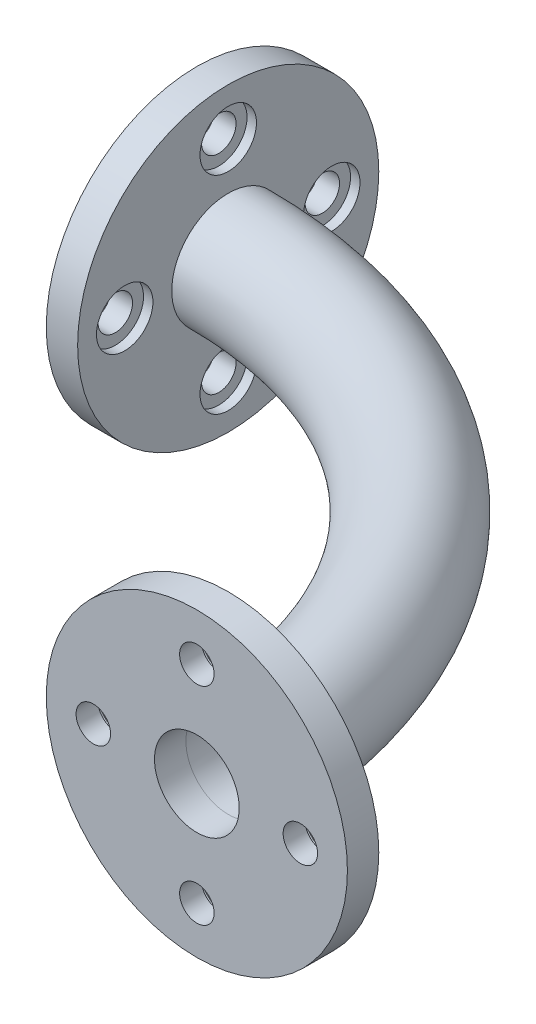
SolidWorks part; units mm, degrees
ref_plane "Alzado" through (0, 0, 0) normal (0, 0, 1) x (1, 0, 0)
ref_plane "Planta" through (0, 0, 0) normal (0, 1, 0) x (1, 0, 0)
ref_plane "Vista lateral" through (0, 0, 0) normal (1, 0, 0) x (0, 0, -1)
sketch "Croquis2" plane through (0, 0, 0) normal (1, 0, 0) x (0, 0, -1)
  circle A0 centre (0, 0) radius 48
  circle A1 centre (0, 0) radius 13.5
  circle A2 centre (0, 33) radius 5.5
  circle A3 centre (33, 0) radius 5.5
  circle A4 centre (0, -33) radius 5.5
  circle A5 centre (-33, 0) radius 5.5
  point P15 (0, 0)
  dimension "D1" = 96
  dimension "D2" = 27
  dimension "D3" = 11
  dimension "D4" = 33
  dimension "D5" = 4
extrude "Saliente-Extruir1" add sketch "Croquis2" along normal blind 10
ref_plane "Plano1" through (0, 0, 150) normal (0, 0, 1) x (1, 0, 0)
sketch "Croquis4" plane through (0, 0, 150) normal (0, 0, 1) x (1, 0, 0)
  circle A0 centre (150, 0) radius 48
  circle A1 centre (150, 0) radius 13.5
  circle A2 centre (150, 33) radius 5.5
  circle A3 centre (183, 0) radius 5.5
  circle A4 centre (150, -33) radius 5.5
  circle A5 centre (117, 0) radius 5.5
  point P5 (0, 0)
  point P6 (171.2712, -22.8328)
  point P7 (0, 0)
  point P11 (150, 0)
  point P16 (150, 0)
  dimension "D1" = 96
  dimension "D2" = 27
  dimension "D3" = 11
  dimension "D4" = 33
  dimension "D5" = 150
  dimension "D6" = 4
extrude "Saliente-Extruir2" add sketch "Croquis4" against normal blind 10 separate body
sketch "Croquis5" plane through (0, 0, 0) normal (0, 1, 0) x (1, 0, 0)
  line L5 (163.5, -140) -> (136.5, -140) construction
  line L7 (163.5, -140) -> (136.5, -140) construction
  line L8 (10, -13.5) -> (10, 13.5) construction
  line L9 (10, -13.5) -> (10, 13.5) construction
  arc A2 (10, 0) -> (150, -140) centre (10, -140) cw
  point P3 (0, 0)
  point P8 (30.5907, -136.617)
  point P11 (150, -140)
  point P14 (10, 0)
  dimension "D1" = 140
sketch "Croquis6" plane through (10, 0, 0) normal (1, 0, 0) x (0, 0, -1)
  line L0 (-13.5, 0) -> (13.5, 0) construction
  circle A0 centre (0, 0) radius 18
  circle A1 centre (0, 0) radius 13.5
  circle A2 centre (0, 0) radius 13.5 construction
  dimension "D1" = 36
sweep "Barrer1" add profiles "Croquis6" path "Croquis5"
sketch "Croquis8" plane through (10, 0, 0) normal (1, 0, 0) x (0, 0, -1)
  circle A0 centre (0, 33) radius 9
  circle A1 centre (33, 0) radius 9
  circle A2 centre (0, -33) radius 9
  circle A3 centre (-33, 0) radius 9
  point P3 (50.4552, 11.7532)
  point P4 (0, 0)
  point P12 (0, 0)
  dimension "D1" = 18
  dimension "D2" = 4
extrude "Cortar-Extruir1" cut sketch "Croquis8" against normal blind 3
sketch "Croquis9" plane through (0, 0, 140) normal (0, 0, -1) x (-1, 0, 0)
  circle A0 centre (-150, 33) radius 9
  circle A1 centre (-117, 0) radius 9
  circle A2 centre (-150, -33) radius 9
  circle A3 centre (-183, 0) radius 9
  circle A4 centre (-183, 0) radius 5.5 construction
  point P3 (26.8309, -109.4995)
  point P4 (0, 0)
  point P5 (-150, -2.8935)
  point P12 (-150, 0)
  point P13 (-182.6685, 0.0603)
  dimension "D1" = 18
  dimension "D2" = 4
extrude "Cortar-Extruir2" cut sketch "Croquis9" against normal blind 3
